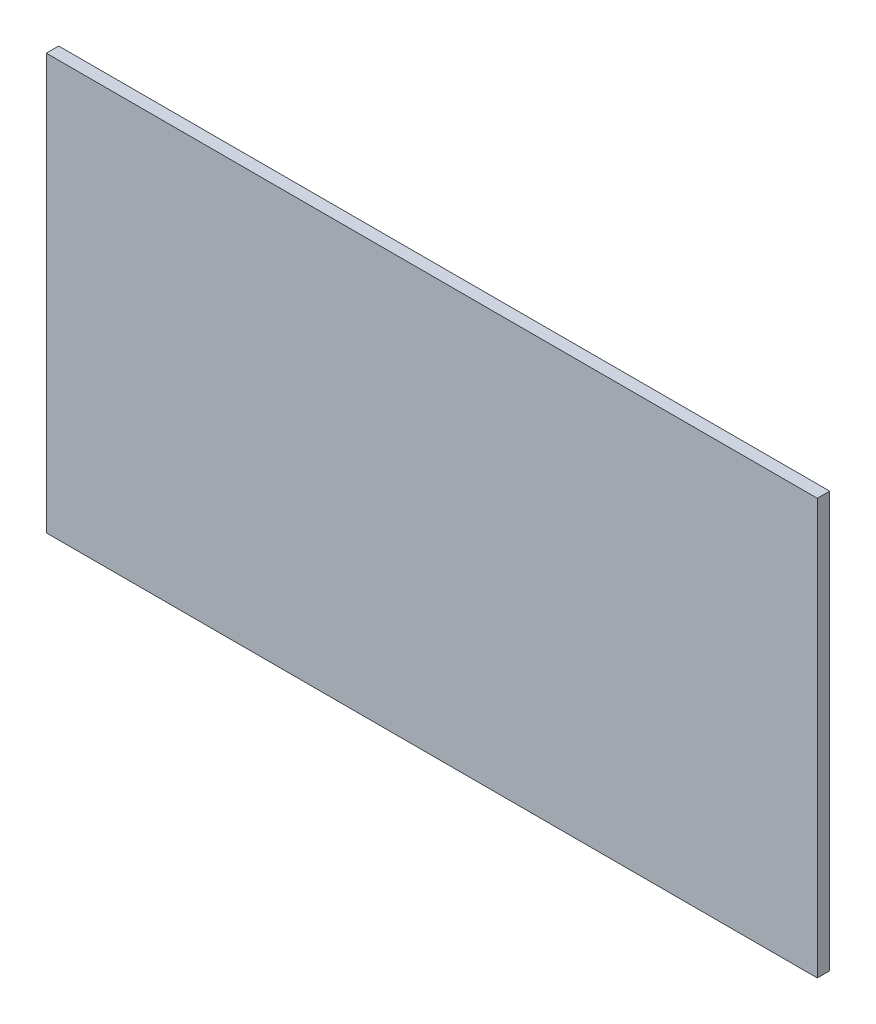
SolidWorks part; units mm, degrees
ref_plane "Front Plane" through (0, 0, 0) normal (0, 0, 1) x (1, 0, 0)
ref_plane "Top Plane" through (0, 0, 0) normal (0, 1, 0) x (1, 0, 0)
ref_plane "Right Plane" through (0, 0, 0) normal (1, 0, 0) x (0, 0, -1)
sketch "Sketch1" plane through (0, 0, 0) normal (0, 0, 1) x (1, 0, 0)
  line L0 (-315.0479, 158.213) -> (-86.0998, 158.213)
  line L1 (-86.0998, 158.213) -> (-5.9689, 158.213)
  line L2 (-5.9689, 158.213) -> (307.1817, 158.213)
  line L3 (307.1817, 158.213) -> (307.1817, -177.067)
  line L4 (307.1817, -177.067) -> (-5.9689, -177.067)
  line L5 (-5.9689, -177.067) -> (-86.0998, -177.067)
  line L6 (-86.0998, -177.067) -> (-315.0479, -177.067)
  line L7 (-315.0479, -177.067) -> (-315.0479, 158.213)
  line L8 (-86.0998, 158.213) -> (-86.0998, -177.067)
  line L9 (-5.9689, 158.213) -> (-5.9689, -177.067)
extrude "Boss-Extrude1" add sketch "Sketch1" along normal blind 10 contours L8 L0 L7 L6 | L9 L1 L8 L5 | L2 L9 L4 L3
